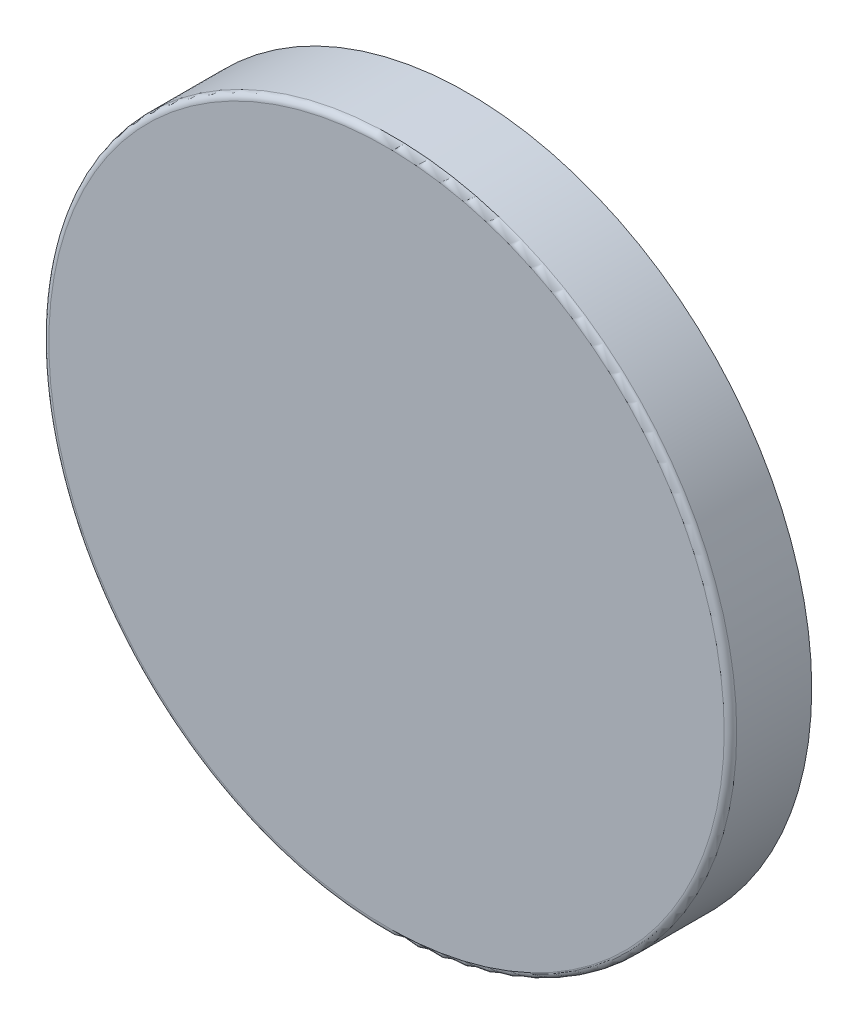
SolidWorks part; units mm, degrees
ref_plane "Front Plane" through (0, 0, 0) normal (0, 0, 1) x (1, 0, 0)
ref_plane "Top Plane" through (0, 0, 0) normal (0, 1, 0) x (1, 0, 0)
ref_plane "Right Plane" through (0, 0, 0) normal (1, 0, 0) x (0, 0, -1)
sketch "Sketch1" plane through (0, 0, 0) normal (0, 0, 1) x (1, 0, 0)
  circle A0 centre (0, 0) radius 55
  dimension "D1" = 110
extrude "Boss-Extrude1" add sketch "Sketch1" along normal blind 13
fillet "Fillet1" radius 1 1 edges at (55, 0, 13)
